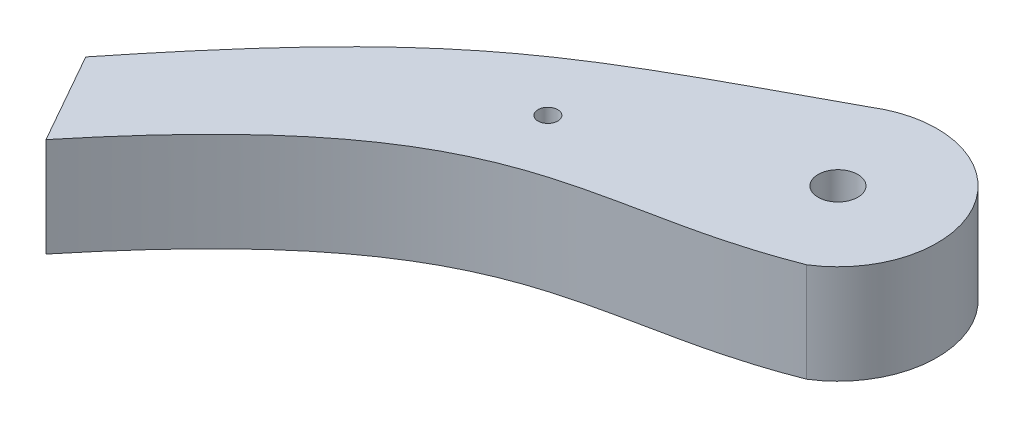
SolidWorks part; units mm, degrees
ref_plane "Front Plane" through (0, 0, 0) normal (0, 0, 1) x (1, 0, 0)
ref_plane "Top Plane" through (0, 0, 0) normal (0, 1, 0) x (1, 0, 0)
ref_plane "Right Plane" through (0, 0, 0) normal (1, 0, 0) x (0, 0, -1)
sketch "Sketch1" plane through (0, 0, 0) normal (0, 1, 0) x (1, 0, 0)
  line L0 (-43.9807, -35.9001) -> (-49.199, -26.6736)
  circle A0 centre (0, 0) radius 2
  arc A1 (5.316, -8.47) -> (-5.316, 8.47) centre (0, 0) ccw
  circle A2 centre (-20.7887, -8.47) radius 1
  spline S0 degree 3 poles (-49.199, -26.6736) (-31.8453, -4.9005) (-24.9667, -2.1396) (-5.316, 8.47) knots 0 0 0 0 1 1 1 1
  spline S1 degree 3 poles (-43.9807, -35.9001) (-21.8126, -8.7402) (-12.0456, -15.2812) (5.316, -8.47) knots 0 0 0 0 1 1 1 1
extrude "Boss-Extrude1" add sketch "Sketch1" along normal blind 10
